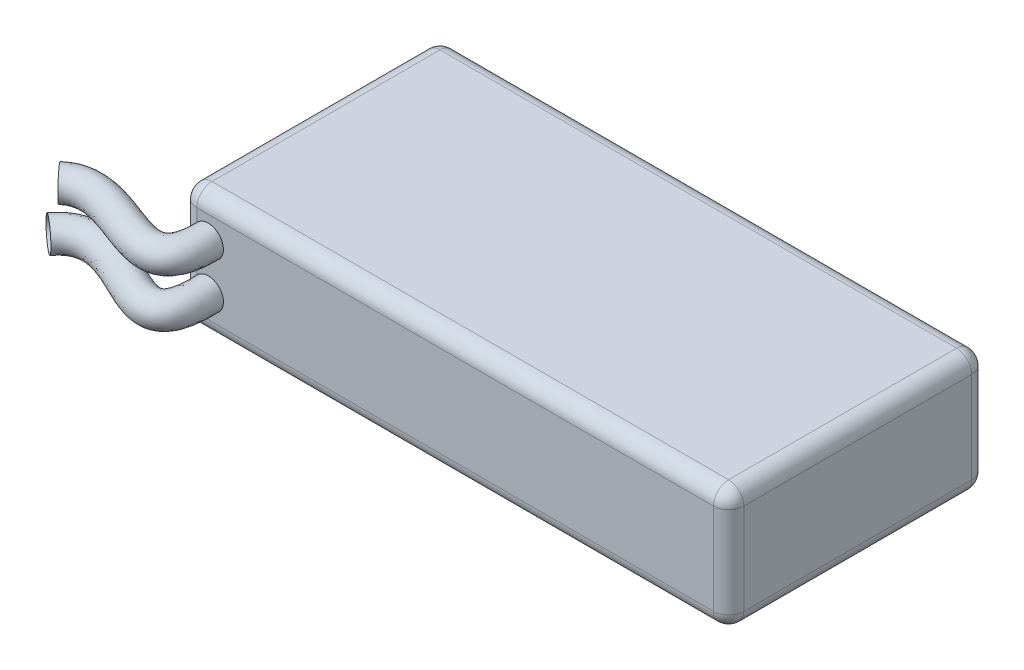
SolidWorks part; units mm, degrees
ref_plane "Front Plane" through (0, 0, 0) normal (0, 0, 1) x (1, 0, 0)
ref_plane "Top Plane" through (0, 0, 0) normal (0, 1, 0) x (1, 0, 0)
ref_plane "Right Plane" through (0, 0, 0) normal (1, 0, 0) x (0, 0, -1)
sketch "Sketch1" plane through (0, 0, 0) normal (0, 1, 0) x (1, 0, 0)
  line L1 (-39.2614, -25.7588) -> (32.7386, -25.7588)
  line L2 (-39.2614, -25.7588) -> (-39.2614, 8.2412)
  line L3 (-39.2614, 8.2412) -> (32.7386, 8.2412)
  line L4 (32.7386, -25.7588) -> (32.7386, 8.2412)
  point P0 (0, 0)
  dimension "D1" = 72
  dimension "D2" = 34
extrude "Boss-Extrude1" add sketch "Sketch1" along normal blind 16
sketch "Sketch2" plane through (0, 0, 25.7588) normal (0, 0, 1) x (1, 0, 0)
  line L0 (-39.2614, 8) -> (-35.7614, 8) construction
  line L1 (-39.2614, 16) -> (-39.2614, 0) construction
  line L2 (-35.7614, 8) -> (-35.7614, 11) construction
  circle A0 centre (-35.7614, 11) radius 2
sketch3d "3DSketch1"
  spline S0 degree 3 poles (-35.7614, 11, 25.7588) (-35.6061, 11, 37.223) (-46.8324, 11, 24.2007) (-52.1473, 11, 28.9888) knots 0 0 0 0 1 1 1 1
surface "Surface-Sweep1"
sketch "Sketch3" plane through (0, 0, 25.7588) normal (0, 0, 1) x (1, 0, 0)
  line L0 (-39.2614, 8) -> (-35.7614, 8) construction
  line L1 (-39.2614, 16) -> (-39.2614, 0) construction
  line L2 (-35.7614, 8) -> (-35.7614, 5) construction
  circle A0 centre (-35.7614, 5) radius 2
sketch3d "3DSketch2"
  spline S0 degree 3 poles (-35.7614, 5, 25.7588) (-35.2664, 5, 39.3984) (-47.3301, 5, 21.8111) (-53.0229, 5, 29.5315) knots 0 0 0 0 1 1 1 1
surface "Surface-Sweep2"
fillet "Fillet1" radius 2 12 edges at (-3.2614, 0, -8.2412) (-39.2614, 0, 8.7588) (-39.2614, 8, -8.2412) (-39.2614, 8, 25.7588) (-39.2614, 16, 8.7588) (-3.2614, 0, 25.7588) (32.7386, 0, 8.7588) (32.7386, 8, -8.2412) (32.7386, 8, 25.7588) (32.7386, 16, 8.7588) (-3.2614, 16, -8.2412) (-3.2614, 16, 25.7588)
